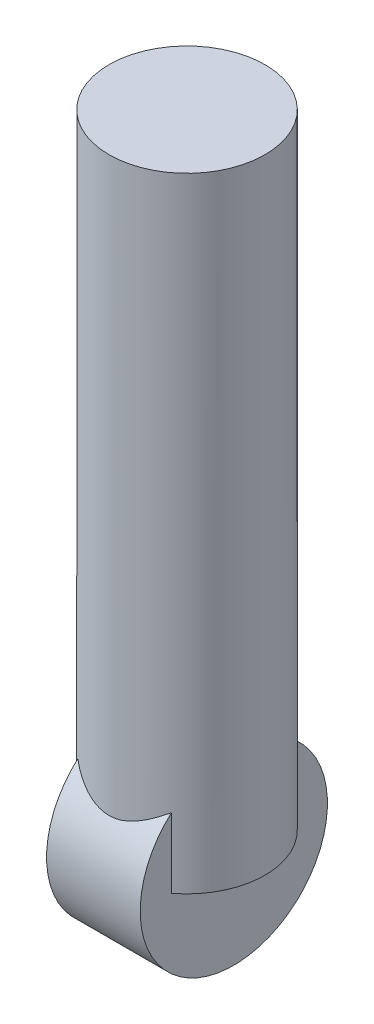
SolidWorks part; units mm, degrees
ref_plane "Front Plane" through (0, 0, 0) normal (0, 0, 1) x (1, 0, 0)
ref_plane "Top Plane" through (0, 0, 0) normal (0, 1, 0) x (1, 0, 0)
ref_plane "Right Plane" through (0, 0, 0) normal (1, 0, 0) x (0, 0, -1)
sketch "Sketch1" plane through (0, 0, 0) normal (0, 1, 0) x (1, 0, 0)
  circle A1 centre (0, 0) radius 25
  dimension "D2" = 50
extrude "Boss-Extrude1" add sketch "Sketch1" along normal blind 200
ref_plane "Plane1" through (0, 230, 0) normal (0, 1, 0) x (1, 0, 0)
sketch "Sketch9" plane through (0, 0, 0) normal (1, 0, 0) x (0, 0, -1)
  circle A0 centre (0, 0) radius 30
  dimension "D1" = 0
extrude "Boss-Extrude4" add sketch "Sketch9" along normal mid plane 30
